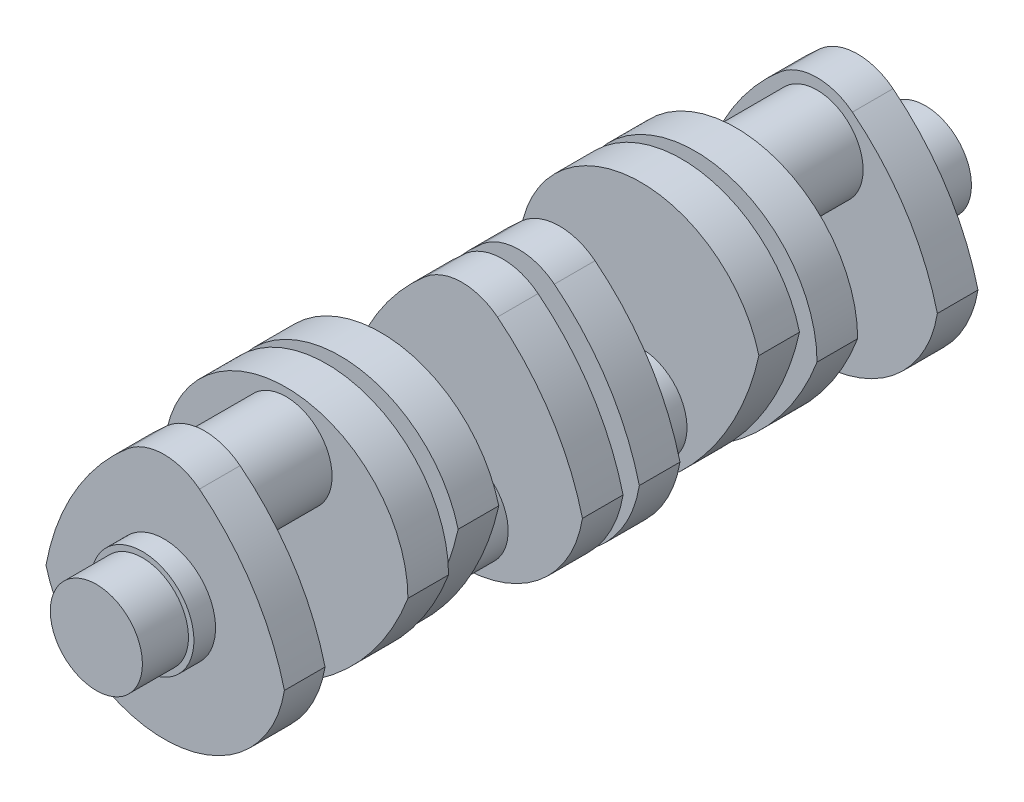
SolidWorks part; units mm, degrees
ref_plane "Ön Düzlem" through (0, 0, 0) normal (0, 0, 1) x (1, 0, 0)
ref_plane "Üst Düzlem" through (0, 0, 0) normal (0, 1, 0) x (1, 0, 0)
ref_plane "Sağ Düzlem" through (0, 0, 0) normal (1, 0, 0) x (0, 0, -1)
sketch "Çizim1" plane through (0, 0, 0) normal (0, 0, 1) x (1, 0, 0)
  circle A0 centre (0, 0) radius 17
extrude "Yükseklik-Ekstrüzyon1" add sketch "Çizim1" along normal blind 25
sketch "Çizim2" plane through (0, 0, 0) normal (0, 0, -1) x (-1, 0, 0)
  circle A0 centre (0, 0) radius 19
extrude "Yükseklik-Ekstrüzyon2" add sketch "Çizim2" against normal blind 8
sketch "Çizim3" plane through (0, 0, 0) normal (0, 0, -1) x (-1, 0, 0)
  arc A0 (-44.4156, -7.2287) -> (43.5844, -11.1982) centre (0, 0) ccw
  arc A1 (13.682, 40.9312) -> (-13.0568, 41.4475) centre (0, 25) ccw
  arc A2 (43.5844, -11.1982) -> (13.682, 40.9312) centre (-44.9553, -27.3452) ccw
  arc A3 (-44.4156, -7.2287) -> (-13.0568, 41.4475) centre (42.901, -29.0417) cw
extrude "Yükseklik-Ekstrüzyon3" add sketch "Çizim3" along normal blind 15
sketch "Çizim4" plane through (0, 0, -15) normal (0, 0, -1) x (-1, 0, 0)
  line L0 (0, 0) -> (0, 25) construction
  circle A0 centre (0, 25) radius 17
extrude "Yükseklik-Ekstrüzyon4" add sketch "Çizim4" along normal blind 30
sketch "Çizim5" plane through (0, 0, -45) normal (0, 0, -1) x (-1, 0, 0)
  arc A0 (45, 0) -> (-45, 0) centre (0, 0) ccw
  arc A2 (-11.9263, -42.2554) -> (11.9263, -42.2554) centre (0, -24.9707) ccw
  arc A3 (45, 0) -> (11.9263, -42.2554) centre (-39.1864, 31.8222) cw
  arc A4 (-45, 0) -> (-11.9263, -42.2554) centre (39.1864, 31.8222) ccw
extrude "Yükseklik-Ekstrüzyon5" add sketch "Çizim5" along normal blind 15
sketch "Çizim6" plane through (0, 0, -60) normal (0, 0, -1) x (-1, 0, 0)
  circle A0 centre (0, 0) radius 17
extrude "Yükseklik-Ekstrüzyon6" add sketch "Çizim6" along normal blind 5
sketch "Çizim7" plane through (0, 0, -65) normal (0, 0, -1) x (-1, 0, 0)
  arc A0 (44.4575, 6.9665) -> (-43.5425, 11.36) centre (0, 0) ccw
  arc A1 (-14.5465, -40.1459) -> (16.9652, -37.3767) centre (0, -25) ccw
  arc A2 (16.9652, -37.3767) -> (44.4575, 6.9665) centre (-56.669, 38.9698) ccw
  arc A3 (-43.5425, 11.36) -> (-14.5465, -40.1459) centre (56.3688, 33.6917) ccw
extrude "Yükseklik-Ekstrüzyon7" add sketch "Çizim7" along normal blind 15
sketch "Çizim9" plane through (0, 0, -80) normal (0, 0, -1) x (-1, 0, 0)
  circle A0 centre (0, -25) radius 17
extrude "Yükseklik-Ekstrüzyon8" add sketch "Çizim9" along normal blind 30
sketch "Çizim10" plane through (0, 0, -110) normal (0, 0, -1) x (-1, 0, 0)
  arc A0 (-44.4156, -7.2287) -> (43.5844, -11.1982) centre (0, 0) ccw
  arc A1 (13.682, 40.9312) -> (-13.0568, 41.4475) centre (0, 25) ccw
  arc A3 (-44.4156, -7.2287) -> (-13.0568, 41.4475) centre (42.901, -29.0417) cw
  arc A4 (43.5844, -11.1982) -> (13.682, 40.9312) centre (-44.9553, -27.3452) ccw
extrude "Yükseklik-Ekstrüzyon9" add sketch "Çizim10" along normal blind 15
sketch "Çizim12" plane through (0, 0, -125) normal (0, 0, -1) x (-1, 0, 0)
  circle A0 centre (0, 0) radius 17
extrude "Yükseklik-Ekstrüzyon10" add sketch "Çizim12" along normal blind 3
mirror "Aynalama1" about plane through (0, 0, -128) normal (0, 0, -1) of bodies 117
